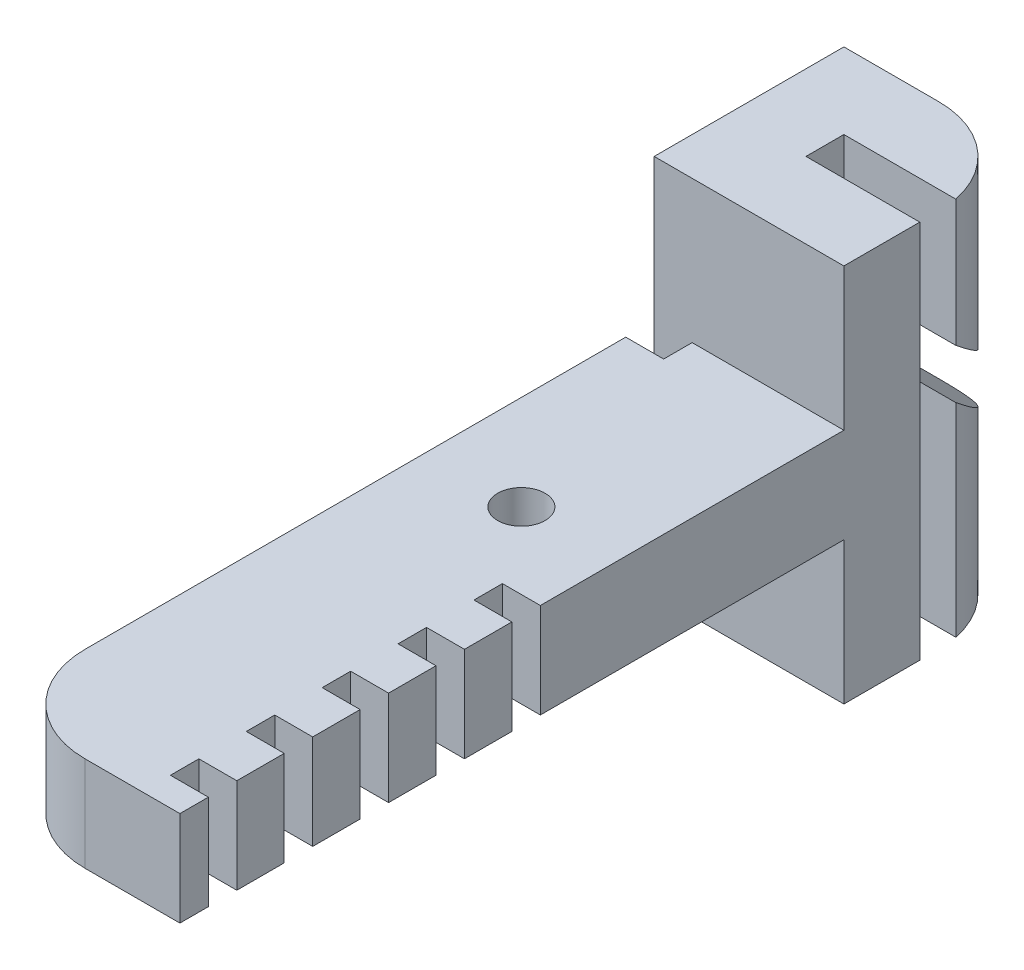
SolidWorks part; units mm, degrees
ref_plane "Front Plane" through (0, 0, 0) normal (0, 0, 1) x (1, 0, 0)
ref_plane "Top Plane" through (0, 0, 0) normal (0, 1, 0) x (1, 0, 0)
ref_plane "Right Plane" through (0, 0, 0) normal (1, 0, 0) x (0, 0, -1)
sketch "Sketch1" plane through (0, 0, 0) normal (0, 1, 0) x (1, 0, 0)
  line L1 (-5, -5) -> (5, -5)
  line L2 (-5, -5) -> (-5, 5)
  line L3 (-5, 5) -> (5, 5)
  line L4 (5, -5) -> (5, 5)
  line L5 (-5, -5) -> (5, 5) construction
  line L6 (-5, 5) -> (5, -5) construction
  point P0 (0, 0)
  dimension "D1" = 10
  dimension "D2" = 10
extrude "Boss-Extrude1" add sketch "Sketch1" along normal mid plane 20
sketch "Sketch2" plane through (0, 0, 5) normal (0, 0, 1) x (1, 0, 0)
  line L0 (5, 10) -> (5, -10) construction
  line L1 (-5, -2.5) -> (5, -2.5)
  line L2 (-5, -2.5) -> (-5, 2.5)
  line L3 (-5, 2.5) -> (5, 2.5)
  line L4 (5, -2.5) -> (5, 2.5)
  line L5 (-5, -2.5) -> (5, 2.5) construction
  line L6 (-5, 2.5) -> (5, -2.5) construction
  point P0 (0, 0)
  dimension "D1" = 5
extrude "Boss-Extrude2" add sketch "Sketch2" along normal blind 35
sketch "Sketch3" plane through (0, 2.5, 0) normal (0, 1, 0) x (1, 0, 0)
  line L1 (5, -5) -> (-5, -5) construction
  circle A0 centre (0, -17) radius 1.25
  dimension "D1" = 2.5
  dimension "D2" = 12
extrude "Cut-Extrude1" cut sketch "Sketch3" against normal up to surface (5 mm away) contours A0 up to face at (0, -2.5, 22.5)
fillet "Fillet1" radius 5 2 edges at (-5, 0, 40) (5, 0, -5)
sketch "Sketch4" plane through (0, 10, 0) normal (0, 1, 0) x (1, 0, 0)
  line L0 (-1, -1) -> (-1, 1)
  line L1 (-1, -1) -> (5, -1)
  line L2 (-1, 1) -> (5, 1)
  line L3 (5, -1) -> (5, 1)
  line L4 (5, -5) -> (5, 0) construction
  dimension "D1" = 2
  dimension "D2" = 6
extrude "Cut-Extrude2" cut sketch "Sketch4" against normal up to surface (20 mm away) up to face at (0.2071, -10, -0.2071)
sketch "Sketch6" plane through (-5, 0, 0) normal (-1, 0, 0) x (0, 0, 1)
  line L0 (5, 2.5) -> (5, -2.5)
  line L1 (5, -2.5) -> (6.5, -2.5)
  line L2 (35, -2.5) -> (5, -2.5) construction
  line L3 (6.5, -2.5) -> (6.5, 2.5)
  line L4 (35, 2.5) -> (5, 2.5) construction
  line L5 (6.5, 2.5) -> (5, 2.5)
  dimension "D1" = 1.5
extrude "Cut-Extrude3" cut sketch "Sketch6" against normal blind 2
sketch "Sketch7" plane through (-1, 0, 0) normal (1, 0, 0) x (0, 0, -1)
  line L0 (-1, 5) -> (11.1033, -5.1559)
  line L1 (-1, -10) -> (-1, 10) construction
  line L2 (11.1033, -5.1559) -> (9.8178, -6.688)
  line L3 (9.8178, -6.688) -> (-1, 2.3892)
  line L4 (-1, -10) -> (-1, 10) construction
  line L5 (1, 10) -> (-1, 10) construction
  line L6 (-1, 5) -> (-1, 2.3892)
  dimension "D1" = 50
  dimension "D2" = 2
  dimension "D3" = 5
extrude "Cut-Extrude4" cut sketch "Sketch7" along normal blind 10
pattern_linear "LPattern1" count 9 spacing 4 along (0, 0, 1) count 2 spacing 8 along (1, 0, 0) skipping (0, 1), (1, 0), (1, 1), (2, 0), (2, 1), (3, 0), (3, 1), (4, 0), (5, 0), (6, 0), (7, 0), (8, 0) of "Cut-Extrude3"
